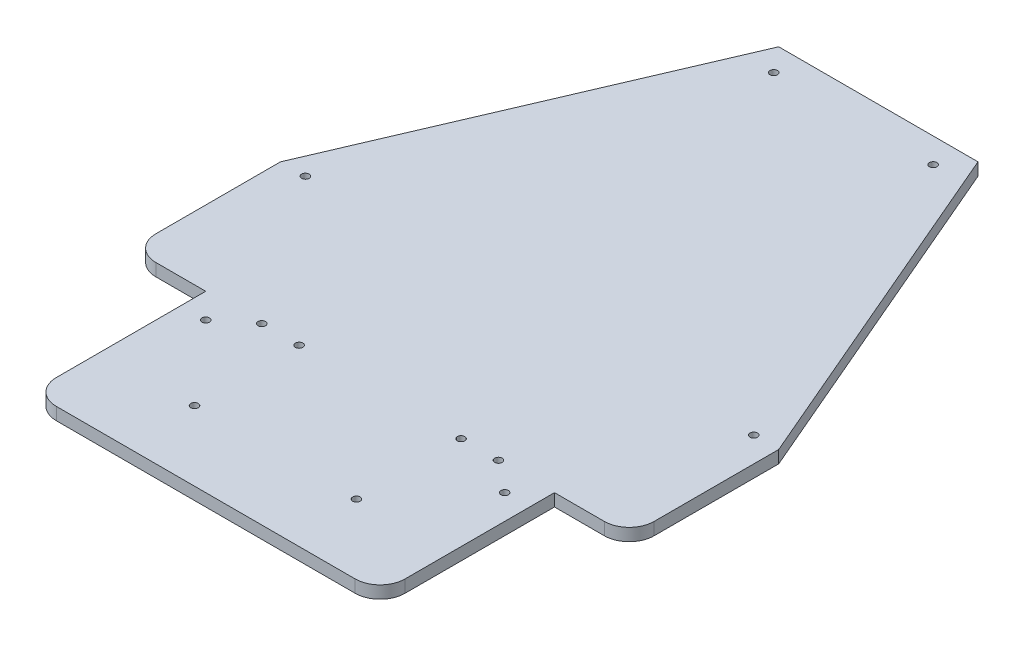
SolidWorks part; units mm, degrees
ref_plane "Front Plane" through (0, 0, 0) normal (0, 0, 1) x (1, 0, 0)
ref_plane "Top Plane" through (0, 0, 0) normal (0, 1, 0) x (1, 0, 0)
ref_plane "Right Plane" through (0, 0, 0) normal (1, 0, 0) x (0, 0, -1)
sketch "Sketch1" plane through (0, 0, 0) normal (0, 1, 0) x (1, 0, 0)
  line L8 (100, -40) -> (100, 10)
  line L10 (-40, 150) -> (40, 150)
  line L11 (40, 150) -> (100, 10)
  line L12 (-40, 150) -> (-100, 10)
  line L13 (-100, -40) -> (-100, 10)
  line L17 (70, -60) -> (70, -50)
  line L18 (70, -50) -> (90, -50)
  line L19 (-70, -60) -> (-70, -50)
  line L20 (-70, -50) -> (-90, -50)
  line L31 (-70, -60) -> (-70, -110)
  line L32 (-60, -120) -> (60, -120)
  line L33 (70, -110) -> (70, -60)
  line L34 (-70, -60) -> (-60, -60) construction
  line L35 (0, -55) -> (0, 55) construction
  arc A6 (90, -50) -> (100, -40) centre (90, -40) ccw
  arc A7 (-90, -50) -> (-100, -40) centre (-90, -40) cw
  arc A8 (60, -120) -> (70, -110) centre (60, -110) ccw
  arc A9 (-70, -110) -> (-60, -120) centre (-60, -110) ccw
  circle A10 centre (-60, -60) radius 1.5
  circle A11 centre (60, -60) radius 1.5
  point P9 (-70, -70)
  point P15 (100, -70)
  point P16 (70, -70)
  point P21 (0, -70)
  point P22 (70, -120)
  point P24 (-100, -70)
  point P26 (-70, -120)
  dimension "D6" = 10
  dimension "D3" = 70
  dimension "D8" = 3
  dimension "D1" = 80
  dimension "D2" = 200
  dimension "D4" = 30
  dimension "D5" = 140
  dimension "D7" = 10
  dimension "D9" = 60
extrude "Boss-Extrude1" add sketch "Sketch1" along normal blind 5
sketch "Sketch8" plane through (0, 5, 0) normal (0, 1, 0) x (1, 0, 0)
  line L2 (-40, 150) -> (-32, 150) construction
  line L3 (40, 150) -> (-40, 150) construction
  line L4 (-32, 150) -> (-32, 140) construction
  line L6 (0, 150) -> (0, 38.0278) construction
  circle A2 centre (-90, 10) radius 1.5
  circle A3 centre (-32, 140) radius 1.5
  circle A6 centre (90, 10) radius 1.5
  circle A7 centre (32, 140) radius 1.5
  dimension "D8" = 3
  dimension "D9" = 3
  dimension "D3" = 8
  dimension "D4" = 10
extrude "Cut-Extrude5" cut sketch "Sketch8" against normal blind 10
sketch "Sketch9" plane through (0, 5, 0) normal (0, 1, 0) x (1, 0, 0)
  line L0 (-70, -50) -> (70, -50) construction
  line L1 (0, -50) -> (40, -50) construction
  line L2 (40, -50) -> (47.5, -50) construction
  line L3 (40, -50) -> (32.5, -50) construction
  line L5 (32.5, -50) -> (32.5, -92) construction
  line L6 (0, -2.75) -> (0, 2.75) construction
  circle A0 centre (47.5, -50) radius 1.5
  circle A1 centre (32.5, -50) radius 1.5
  circle A4 centre (32.5, -92) radius 1.5
  circle A5 centre (-32.5, -50) radius 1.5
  circle A6 centre (-32.5, -92) radius 1.5
  circle A7 centre (-47.5, -50) radius 1.5
  dimension "D2" = 7.5
  dimension "D4" = 3
  dimension "D5" = 3
  dimension "D6" = 42
  dimension "D7" = 3
  dimension "D1" = 40
  dimension "D3" = 7.5
extrude "Cut-Extrude6" cut sketch "Sketch9" against normal blind 10
